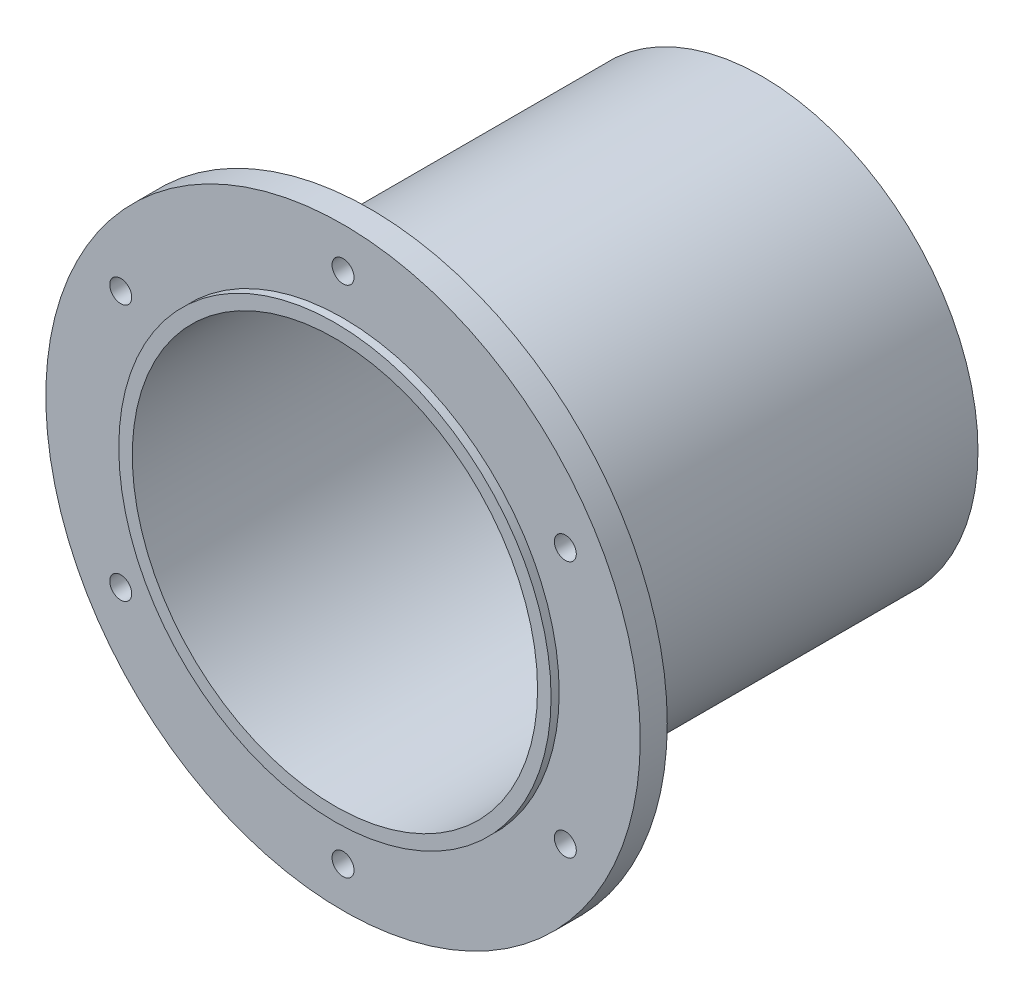
SolidWorks part; units mm, degrees
ref_plane "Front Plane" through (0, 0, 0) normal (0, 0, 1) x (1, 0, 0)
ref_plane "Top Plane" through (0, 0, 0) normal (0, 1, 0) x (1, 0, 0)
ref_plane "Right Plane" through (0, 0, 0) normal (1, 0, 0) x (0, 0, -1)
sketch "Sketch1" plane through (0, 0, 0) normal (0, 0, 1) x (1, 0, 0)
  circle A0 centre (0, 0) radius 69.85
  circle A1 centre (0, 0) radius 50.8
  circle A2 centre (0, 60.325) radius 2.5794
  circle A3 centre (-52.243, 30.1625) radius 2.5794
  circle A4 centre (-52.243, -30.1625) radius 2.5794
  circle A5 centre (0, -60.325) radius 2.5794
  circle A6 centre (52.243, -30.1625) radius 2.5794
  circle A7 centre (52.243, 30.1625) radius 2.5794
extrude "Extrude1" add sketch "Sketch1" along normal blind 6.35
sketch "Sketch2" plane through (0, 0, 0) normal (0, 0, 1) x (1, 0, 0)
  circle A0 centre (0, 0) radius 47.625
  circle A1 centre (0, 0) radius 50.8
extrude "Extrude2" add sketch "Sketch2" along normal blind 8.255 and the other way blind 92.075
